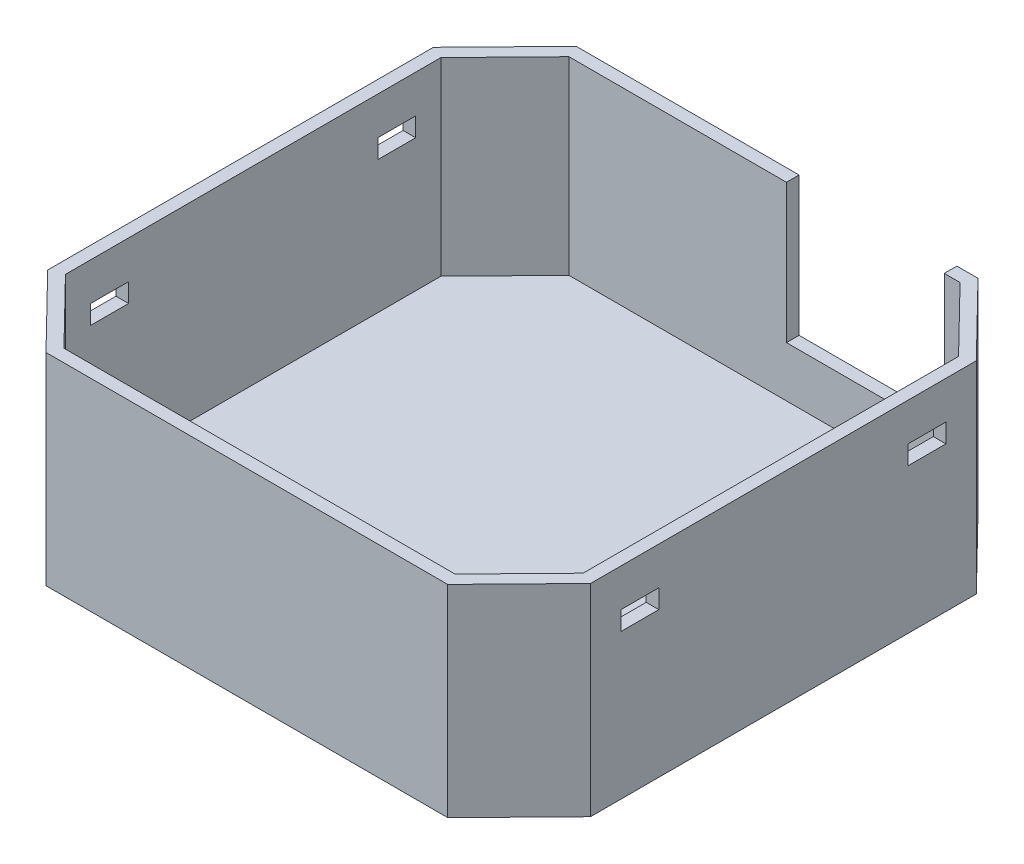
SolidWorks part; units mm, degrees
ref_plane "Front Plane" through (0, 0, 0) normal (0, 0, 1) x (1, 0, 0)
ref_plane "Top Plane" through (0, 0, 0) normal (0, 1, 0) x (1, 0, 0)
ref_plane "Right Plane" through (0, 0, 0) normal (1, 0, 0) x (0, 0, -1)
sketch "Sketch1" plane through (0, 0, 0) normal (0, 1, 0) x (1, 0, 0)
  line L1 (-21.5, 21) -> (21.5, 21) construction
  line L3 (-21.5, -21) -> (21.5, -21) construction
  line L4 (21.5, 21) -> (21.5, -21) construction
  line L5 (21.5, -21) -> (-21.5, 21) construction
  line L6 (21.5, 21) -> (-21.5, -21) construction
  line L16 (-21.5, 21) -> (-21.5, -21) construction
  line L18 (-21.5, 15.277) -> (-15.9101, 21)
  line L26 (-21.5, -15.277) -> (-15.9101, -21)
  line L27 (21.5, -15.277) -> (15.9101, -21)
  line L28 (21.5, 15.277) -> (15.9101, 21)
  line L29 (21.5, -15.277) -> (21.5, 15.277)
  line L30 (15.9101, -21) -> (-15.9101, -21)
  line L31 (-15.9101, 21) -> (15.9101, 21)
  line L32 (-21.5, 15.277) -> (-21.5, -15.277)
  point P6 (0, 0)
  dimension "D1" = 42
  dimension "D2" = 43
  dimension "D3" = 8
  dimension "D4" = 8
  dimension "D5" = 8
  dimension "D6" = 8
extrude "Boss-Extrude1" add sketch "Sketch1" along normal blind 16
sketch "Sketch2" plane through (0, 16, 0) normal (0, 1, 0) x (1, 0, 0)
  line L55 (-15.489, 20) -> (-20.5, 14.8697)
  line L56 (15.489, 20) -> (-15.489, 20)
  line L57 (20.5, 14.8697) -> (15.489, 20)
  line L58 (20.5, -14.8697) -> (20.5, 14.8697)
  line L59 (15.489, -20) -> (20.5, -14.8697)
  line L60 (-15.489, -20) -> (15.489, -20)
  line L61 (-20.5, -14.8697) -> (-15.489, -20)
  line L62 (-20.5, 14.8697) -> (-20.5, -14.8697)
  line L63 (-15.489, 20) -> (-20.5, 14.8697)
  line L64 (15.489, 20) -> (-15.489, 20)
  line L65 (20.5, 14.8697) -> (15.489, 20)
  line L66 (20.5, -14.8697) -> (20.5, 14.8697)
  line L67 (15.489, -20) -> (20.5, -14.8697)
  line L68 (-15.489, -20) -> (15.489, -20)
  line L69 (-20.5, -14.8697) -> (-15.489, -20)
  line L70 (-20.5, 14.8697) -> (-20.5, -14.8697)
  dimension "D1" = 1
extrude "Cut-Extrude1" cut sketch "Sketch2" against normal blind 15
sketch "Sketch3" plane through (0, 16, 0) normal (0, 1, 0) x (1, 0, 0)
  line L0 (14.239, 21) -> (14.239, 20)
  line L1 (20.5, -14.8697) -> (20.5, 14.8697) construction
  line L2 (15.489, 20) -> (-15.489, 20) construction
  line L3 (14.239, 20) -> (1.739, 20)
  line L5 (1.739, 20) -> (1.739, 21)
  line L6 (1.739, 21) -> (14.239, 21)
  line L7 (15.9101, 21) -> (-15.9101, 21) construction
  line L8 (15.489, 20) -> (-15.489, 20) construction
  circle A0 centre (16.5, 12.2716) radius 1.0029
  point P9 (14.489, 21)
  point P11 (0, 0)
  point P12 (1.2152, 20)
  point P14 (1.489, 20)
  dimension "D1" = 12.5
  dimension "D2" = 1.25
  dimension "D3" = 4
extrude "Cut-Extrude2" cut sketch "Sketch3" against normal blind 11
sketch "Sketch4" plane through (-21.5, 0, 0) normal (-1, 0, 0) x (0, 0, 1)
  line L1 (-12.8697, 11.5) -> (-9.8697, 11.5)
  line L2 (-12.8697, 11.5) -> (-12.8697, 13)
  line L3 (-12.8697, 13) -> (-9.8697, 13)
  line L4 (-9.8697, 11.5) -> (-9.8697, 13)
  line L5 (-12.8697, 11.5) -> (-9.8697, 13) construction
  line L6 (-12.8697, 13) -> (-9.8697, 11.5) construction
  line L8 (0, -7.2974) -> (0, 20.2455) construction
  line L9 (12.8697, 13) -> (9.8697, 13)
  line L10 (9.8697, 11.5) -> (9.8697, 13)
  line L11 (12.8697, 11.5) -> (9.8697, 11.5)
  line L12 (12.8697, 11.5) -> (12.8697, 13)
  line L13 (-14.8697, 1) -> (-14.8697, 16) construction
  line L14 (-14.8697, 16) -> (14.8697, 16) construction
  point P0 (-11.3697, 12.25)
  point P16 (0, 20.2455)
  dimension "D1" = 3
  dimension "D2" = 1.5
  dimension "D3" = 3
  dimension "D4" = 2
extrude "Cut-Extrude3" cut sketch "Sketch4" against normal through all both and the other way through all
sketch "Sketch5" plane through (0, 1, 0) normal (0, 1, 0) x (1, 0, 0)
  line L0 (20.5, -14.8697) -> (20.5, 14.8697) construction
  line L1 (15.489, 20) -> (-15.489, 20) construction
  circle A0 centre (16, 13) radius 1
  circle A1 centre (8.5, 17) radius 0.75
  dimension "D1" = 4.5
  dimension "D3" = 2
  dimension "D4" = 7.5
  dimension "D6" = 1.5
  dimension "D2" = 7
  dimension "D5" = 4
extrude "Cut-Extrude4" cut sketch "Sketch5" against normal up to surface (1 mm away) up to face at (0, 0, 0)
